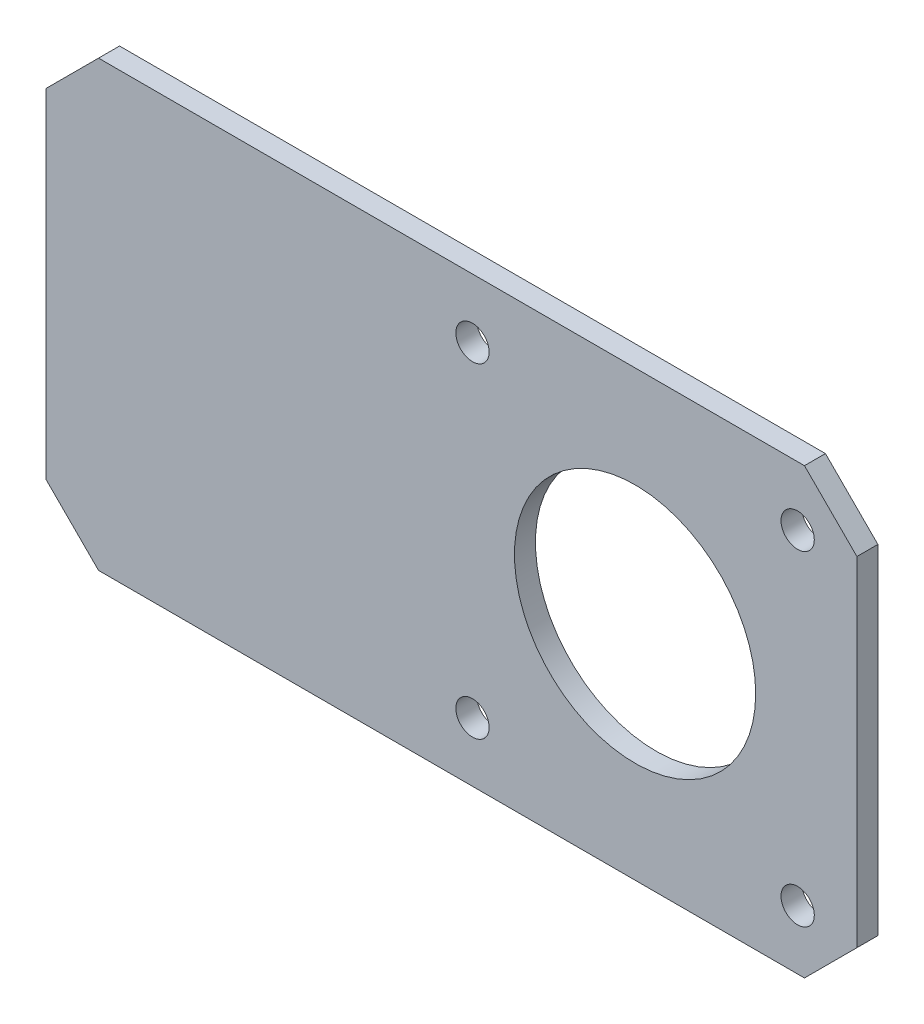
SolidWorks part; units mm, degrees
ref_plane "Front Plane" through (0, 0, 0) normal (0, 0, 1) x (1, 0, 0)
ref_plane "Top Plane" through (0, 0, 0) normal (0, 1, 0) x (1, 0, 0)
ref_plane "Right Plane" through (0, 0, 0) normal (1, 0, 0) x (0, 0, -1)
sketch "Sketch1" plane through (0, 0, 0) normal (0, 0, 1) x (1, 0, 0)
  line L1 (-21.15, -21.15) -> (21.15, -21.15)
  line L2 (-21.15, -21.15) -> (-21.15, 21.15)
  line L3 (-21.15, 21.15) -> (21.15, 21.15)
  line L4 (21.15, -21.15) -> (21.15, 21.15)
  line L5 (-21.15, -21.15) -> (21.15, 21.15) construction
  line L6 (-21.15, 21.15) -> (21.15, -21.15) construction
  line L7 (-21.15, 21.15) -> (-56.15, 21.15)
  line L8 (-21.15, 21.15) -> (-21.15, -21.15)
  line L9 (-21.15, -21.15) -> (-56.15, -21.15)
  line L10 (-56.15, 21.15) -> (-56.15, -21.15)
  line L11 (-38.65, -21.15) -> (-38.65, 21.15) construction
  line L12 (-21.15, 0) -> (-56.15, 0) construction
  point P0 (0, 0)
  point P13 (-38.65, 0)
  dimension "D1" = 42.3
  dimension "D2" = 42.3
  dimension "D3" = 35
extrude "Boss-Extrude1" add sketch "Sketch1" along normal blind 2 contours L7 L10 L9 L2 | L1 L4 L3 L2
hole_wizard "1/8 (0.125) Diameter Hole1" positions "Sketch3" profile "Sketch2" hole size "1/8" standard "ANSI Inch"
sketch "Sketch3" plane through (0, 0, 2) normal (0, 0, 1) x (1, 0, 0)
  line L0 (-15.5, 15.5) -> (15.5, -15.5) construction
  point P0 (-15.5, 15.5)
  point P2 (15.5, 15.5)
  point P4 (15.5, -15.5)
  point P6 (-15.5, -15.5)
  dimension "D1" = 31
  dimension "D2" = 31
sketch "Sketch2" plane through (-15.5, 15.5, 2) normal (1, 0, 0) x (0, -1, 0)
  line L0 (0, 0) -> (0, 5.4539)
  line L1 (0, 5.4539) -> (1.5875, 4.5)
  line L2 (1.5875, 4.5) -> (1.5875, 0)
  line L5 (1.5875, 0) -> (0, 0)
  line L10 (0, 5.4539) -> (-1.5875, 4.5) construction
  line L11 (0, -6.35) -> (0, 107.95) construction
  dimension "Hole Dia." = 3.175
  dimension "Hole Depth" = 4.5
  dimension "Drill Angle" = 118
sketch "Sketch4" plane through (0, 0, 2) normal (0, 0, 1) x (1, 0, 0)
  circle A0 centre (0, 0) radius 11.5
  dimension "D1" = 23
extrude "Cut-Extrude1" cut sketch "Sketch4" against normal blind 2 contours A0
chamfer "Chamfer1" distance 5 angle 45 4 edges at (21.15, -21.15, 1) (21.15, 21.15, 1) (-56.15, 21.15, 1) (-56.15, -21.15, 1)
